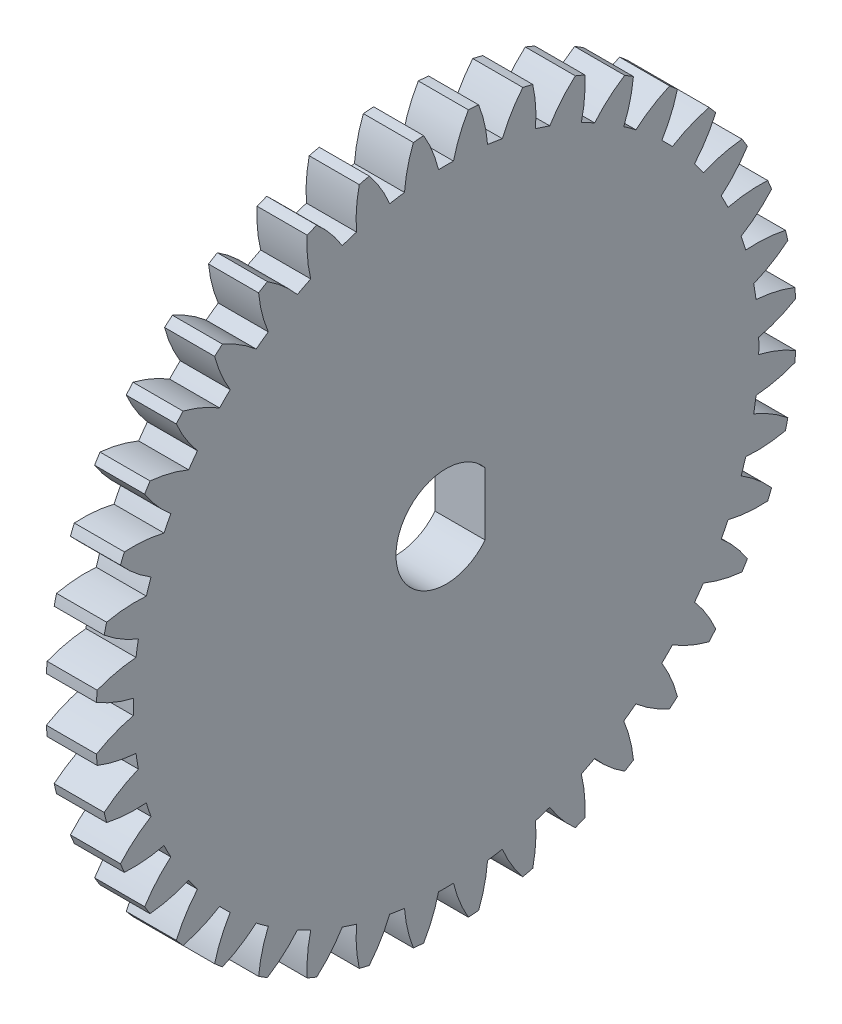
SolidWorks part; units mm, degrees
ref_plane "Plane1" through (0, 0, 0) normal (0, 0, 1) x (1, 0, 0)
ref_plane "Plane2" through (0, 0, 0) normal (0, 1, 0) x (1, 0, 0)
ref_plane "Plane3" through (0, 0, 0) normal (1, 0, 0) x (0, 0, -1)
sketch "HoldingSke" plane through (0, 0, 0) normal (0, 1, 0) x (1, 0, 0)
  line L0 (0, 0) -> (0.766, -0.6428)
  line L1 (-15, 0) -> (100, 0) construction
  line L2 (0, 0) -> (-2.1039, 2.3779)
  line L3 (0, 0) -> (-11.863, 4.5341)
  line L4 (0, 0) -> (6.6156, 5.5511)
  line L5 (0, 0) -> (-46.8476, -17.4728)
  line L6 (0, 0) -> (-2.4869, -1.6779)
  line L7 (-2.1039, 2.3779) -> (8.6588, 51.207)
  line L8 (-76.2, 54.61) -> (-75.2, 54.61)
  line L9 (-71.009, 38.7566) -> (-53.1078, 45.2721)
  line L10 (-76.2, 71.12) -> (104.1128, 71.12)
  line L11 (0, 0) -> (-3, 0)
  line L12 (-76.2, 101.6) -> (-76.162, 101.6)
  line L13 (24.9733, 27.94) -> (52.9518, 28.4284)
  line L14 (24.9733, 27.94) -> (24.9743, 27.94)
  line L15 (24.9733, 27.94) -> (100.4006, 29.5858)
  line L16 (-63.627, -1) -> (-12.827, -1)
  circle A0 centre (0, 0) radius 3
  circle A1 centre (0, 0) radius 18.749
  circle A2 centre (0, 0) radius 37.5
  circle A3 centre (0, 0) radius 3
  dimension "MHD" = 37.498
  dimension "Hub_dia" = 75
  dimension "Bore" = 6
  dimension "MBD" = 6
  dimension "Num_teeth" = 40
  dimension "Pitch" = 1
  dimension "Overall_len" = 50
  dimension "Show_teeth" = 40
  dimension "Thickness" = 3
  dimension "OAL" = 50.0012
  dimension "T_dim" = 1
  dimension "Ap" = 20
  dimension "H" = 19.05
  dimension "Pitch_radius" = 180.3128
  dimension "Width" = 3
  dimension "Backlash" = 0.038
  dimension "Addendum_fac" = 1
  dimension "Dedendum_fac" = 1.25
  dimension "Clearance_fac" = 0.25
  dimension "Dedendum_add" = 0.001
  dimension "Module" = 1
sketch "BasProSke" plane through (0, 0, 0) normal (0, 1, 0) x (1, 0, 0)
  line L0 (-10, 0) -> (60, 0) construction
  line L1 (0, 0) -> (0, 21)
  line L2 (0, 0) -> (3, 0)
  line L3 (3, 0) -> (3, 21)
  line L4 (3, 21) -> (0, 21)
  dimension "Thickness" = 3
  dimension "Diameter" = 42
revolve "Base-Revolve" add sketch "BasProSke" angle 360 about L0
sketch "TooCutSke" plane through (0, 0, 0) normal (1, 0, 0) x (0, 0, -1)
  line L1 (0, 0) -> (0, 107) construction
  line L2 (0, 0) -> (-0.8517, 19.9819) construction
  line L3 (0, 0) -> (-3.1363, 39.8509) construction
  line L4 (-0.8517, 19.9819) -> (-1.5682, 19.9255) construction
  arc A0 (0.4487, 18.7436) -> (-0.4487, 18.7436) centre (0, 0) ccw
  arc A1 (1.3547, 20.9817) -> (-1.3547, 20.9817) centre (0, 0) ccw
  circle A2 centre (0, 0) radius 20 construction
  circle A3 centre (0, 0) radius 18.7939 construction
  arc A4 (-0.4487, 18.7436) -> (-1.3547, 20.9817) centre (-8.2322, 16.895) ccw
  arc A5 (1.3547, 20.9817) -> (0.4487, 18.7436) centre (8.2322, 16.895) ccw
  dimension "Root_dia" = 37.498
  dimension "Overcut_dia" = 42.0508
  dimension "Pitch_dia" = 40
  dimension "Base_dia" = 37.5877
  dimension "Flank_rad" = 8
  dimension "Half_ang" = 4.5
  dimension "Half_CT" = 0.7187
extrude "ToothCut" cut sketch "TooCutSke" along normal through all
fillet "Breaks" [suppressed] radius 0.02
fillet "RootFillets" [suppressed] radius 0.251
pattern_circular "TeethCuts" count 40 every 9 about axis through (-10, 0, 0) along (1, 0, 0) of "ToothCut", "RootFillets", "Breaks"
sketch "HubNeaOneSke" plane through (0, 0, 0) normal (-1, 0, 0) x (0, 0, 1)
  circle A0 centre (0, 0) radius 18.749
  dimension "Diameter" = 37.498
extrude "HubNearOne" [suppressed] add sketch "HubNeaOneSke" along normal blind 47.0012
sketch "HubNeaBotSke" plane through (0, 0, 0) normal (-1, 0, 0) x (0, 0, 1)
  circle A0 centre (0, 0) radius 18.749
  dimension "Diameter" = 37.498
extrude "HubNearBoth" [suppressed] add sketch "HubNeaBotSke" along normal blind 23.5006
ref_plane "FarPln" through (3, 0, 0) normal (1, 0, 0) x (0, 0, -1)
sketch "HubFarSke" plane through (3, 0, 0) normal (1, 0, 0) x (0, 0, -1)
  circle A0 centre (0, 0) radius 18.749
  dimension "Diameter" = 37.498
extrude "HubFar" [suppressed] add sketch "HubFarSke" along normal blind 23.5006
sketch "BorSke" plane through (0, 0, 0) normal (1, 0, 0) x (0, 0, -1)
  circle A0 centre (0, 0) radius 1.5
  dimension "Diameter" = 3
extrude "Bore" cut sketch "BorSke" along normal mid plane 100.0024
sketch "KeySke" plane through (0, 0, 0) normal (1, 0, 0) x (0, 0, -1)
  line L0 (-1, 0) -> (-1, 4)
  line L1 (-1, 4) -> (1, 4)
  line L2 (1, 4) -> (1, 0)
  line L3 (0, 0) -> (0, 34) construction
  line L4 (-1, 0) -> (1, 0)
  dimension "Offset" = 4
  dimension "Width" = 2
extrude "Keyway" [suppressed] cut sketch "KeySke" along normal mid plane 100.0024
pattern_circular "Keyway2" [suppressed] count 2 every 90 about axis through (-10, 0, 0) along (1, 0, 0)
sketch "Sketch1" plane through (3, 0, 0) normal (1, 0, 0) x (0, 0, -1)
  line L0 (2.3419, -1.875) -> (2.3419, 1.875)
  arc A0 (2.3419, 1.875) -> (2.3419, -1.875) centre (0, 0) ccw
  dimension "D1" = 3.75
  dimension "D2" = 6
extrude "Cut-Extrude1" cut sketch "Sketch1" against normal through all
equation "' \"Module@HoldingSke\" = 6.35"
equation "' \"Num_teeth@HoldingSke\" = 12"
equation "' \"Ap@HoldingSke\" =  20"
equation "' \"Ap@HoldingSke\" = 20"
equation "' \"Width@HoldingSke\" = 0.5 * 25.4"
equation "' \"Hub_dia@HoldingSke\"= 1 * 25.4"
equation "' \"Hub_dia@HoldingSke\" = 1 * 25.4"
equation "' \"Overall_len@HoldingSke\" = 1.0 * 25.4"
equation "' \"T_dim@HoldingSke\" = 0.1 * 25.4"
equation "' \"Width@KeySke\" = 0.25 * 25.4"
equation "' \"Show_teeth@HoldingSke\" = 13"
equation "' \"Backlash@HoldingSke\" = 0.009 * 25.4"
equation "' \"Addendum_fac@HoldingSke\" = 1.0"
equation "' \"Dedendum_fac@HoldingSke\" = 1.25"
equation "' \"Dedendum_add@HoldingSke\" = 0.00005 * 25.4"
equation "' \"Clearance_fac@HoldingSke\" = 0.25"
equation "\"Pitch@HoldingSke\" = 1 / \"Module@HoldingSke\""
equation "\"Overcut_dia@TooCutSke\" = (\"Num_teeth@HoldingSke\" + 2 * \"Addendum_fac@HoldingSke\") / \"Pitch@HoldingSke\" + 0.002 * 25.4"
equation "\"Pitch_dia@TooCutSke\" = \"Num_teeth@HoldingSke\" / \"Pitch@HoldingSke\""
equation "\"Base_dia@TooCutSke\" = \"Num_teeth@HoldingSke\" / \"Pitch@HoldingSke\" * cos((\"Ap@HoldingSke\"  * 3.14159265 / 180))"
equation "\"Root_dia@TooCutSke\" = (\"Num_teeth@HoldingSke\" + 2) / \"Pitch@HoldingSke\" - 2 * (\"Addendum_fac@HoldingSke\" + \"Dedendum_fac@HoldingSke\") / \"Pitch@HoldingSke\" - \"Dedendum_add@HoldingSke\" * 2"
equation "\"Half_ang@TooCutSke\" = 180 / \"Num_teeth@HoldingSke\""
equation "\"Half_CT@TooCutSke\" = \"Num_teeth@HoldingSke\" / \"Pitch@HoldingSke\" * sin((3.14159265 / 2 / \"Num_teeth@HoldingSke\")) / 2 - 7 * \"Backlash@HoldingSke\" / 4"
equation "\"Flank_rad@TooCutSke\" = \"Num_teeth@HoldingSke\" / \"Pitch@HoldingSke\" / 5"
equation "\"Radius@RootFillets\" = \"Clearance_fac@HoldingSke\" / \"Pitch@HoldingSke\" + \"Dedendum_add@HoldingSke\""
equation "\"Break_rad@Breaks\" = 0.02 / \"Pitch@HoldingSke\""
equation "\"Thickness@HoldingSke\" = \"Width@HoldingSke\""
equation "\"OAL@HoldingSke\" = \"Thickness@HoldingSke\""
equation "\"MHD@HoldingSke\" = (\"Num_teeth@HoldingSke\" + 2) / \"Pitch@HoldingSke\" - 2 * (\"Addendum_fac@HoldingSke\" + \"Dedendum_fac@HoldingSke\")  / \"Pitch@HoldingSke\" - \"Dedendum_add@HoldingSke\" * 2"
equation "\"MBD@HoldingSke\" = (\"Num_teeth@HoldingSke\" + 2) / \"Pitch@HoldingSke\" - 2 * (\"Addendum_fac@HoldingSke\" + \"Dedendum_fac@HoldingSke\")  / \"Pitch@HoldingSke\" - \"Dedendum_add@HoldingSke\" * 2 - 0.002 * 25.4"
equation "\"MHD@HoldingSke\" = ((sgn( \"MHD@HoldingSke\" - \"Hub_dia@HoldingSke\" )-1)*( \"MHD@HoldingSke\" - \"Hub_dia@HoldingSke\" ))/-2+ \"Hub_dia@HoldingSke\""
equation "\"MBD@HoldingSke\" = ((sgn( \"MBD@HoldingSke\" - \"Bore@HoldingSke\" )-1)*( \"MBD@HoldingSke\" - \"Bore@HoldingSke\" ))/-2+ \"Bore@HoldingSke\""
equation "\"OAL@HoldingSke\" = ((sgn( \"OAL@HoldingSke\" - \"Overall_len@HoldingSke\" )+1)*( \"OAL@HoldingSke\" - \"Overall_len@HoldingSke\" ))/2 + \"Overall_len@HoldingSke\" + 0.000002 * 25.4"
equation "\"Num_teeth@TeethCuts\" = int( \"Show_teeth@HoldingSke\" ) + 1"
equation "\"Num_teeth@TeethCuts\" = ((sgn( \"Num_teeth@TeethCuts\" - \"Num_teeth@HoldingSke\" )-1)*( \"Num_teeth@TeethCuts\" - \"Num_teeth@HoldingSke\" ))/-2+ \"Num_teeth@HoldingSke\""
equation "\"Num_teeth@TeethCuts\" = ((sgn( \"Num_teeth@TeethCuts\" - 2.0)+1)*( \"Num_teeth@TeethCuts\" - 2.0))/2 +2.0"
equation "\"Angle@TeethCuts\" = 360.0 / \"Num_teeth@HoldingSke\""
equation "\"Diameter@BasProSke\" = (\"Num_teeth@HoldingSke\" + 2 * \"Addendum_fac@HoldingSke\") / \"Pitch@HoldingSke\""
equation "\"Thickness@BasProSke\"  = \"Thickness@HoldingSke\""
equation "' \"Fillet_rad@BasProSke\" =  \"Thickness@HoldingSke\" * 0.05"
equation "' \"Fillet_rad@BasProSke\" = \"Thickness@HoldingSke\" * 0.05"
equation "\"MHD@HoldingSke\" = ((sgn( \"MHD@HoldingSke\" - \"Root_dia@TooCutSke\" )-1)*( \"MHD@HoldingSke\" - \"Root_dia@TooCutSke\" ))/-2+ \"Root_dia@TooCutSke\""
equation "\"Diameter@HubNeaOneSke\" = \"MHD@HoldingSke\""
equation "\"Length@HubNearOne\" = \"OAL@HoldingSke\" - \"Thickness@BasProSke\""
equation "\"Diameter@HubNeaBotSke\" = \"MHD@HoldingSke\""
equation "\"Length@HubNearBoth\" = ( \"OAL@HoldingSke\" - \"Thickness@BasProSke\" ) / 2.0"
equation "\"Thickness@FarPln\" = \"Thickness@BasProSke\""
equation "\"Diameter@HubFarSke\" = \"MHD@HoldingSke\""
equation "\"Length@HubFar\" = ( \"OAL@HoldingSke\" - \"Thickness@BasProSke\" ) / 2.0"
equation "\"D1@Bore\" = \"OAL@HoldingSke\" * 2.0"
equation "\"D1@Keyway\" = \"OAL@HoldingSke\" * 2.0"
equation "\"Offset@KeySke\" = \"T_dim@HoldingSke\" + \"MBD@HoldingSke\" / 2.0"
